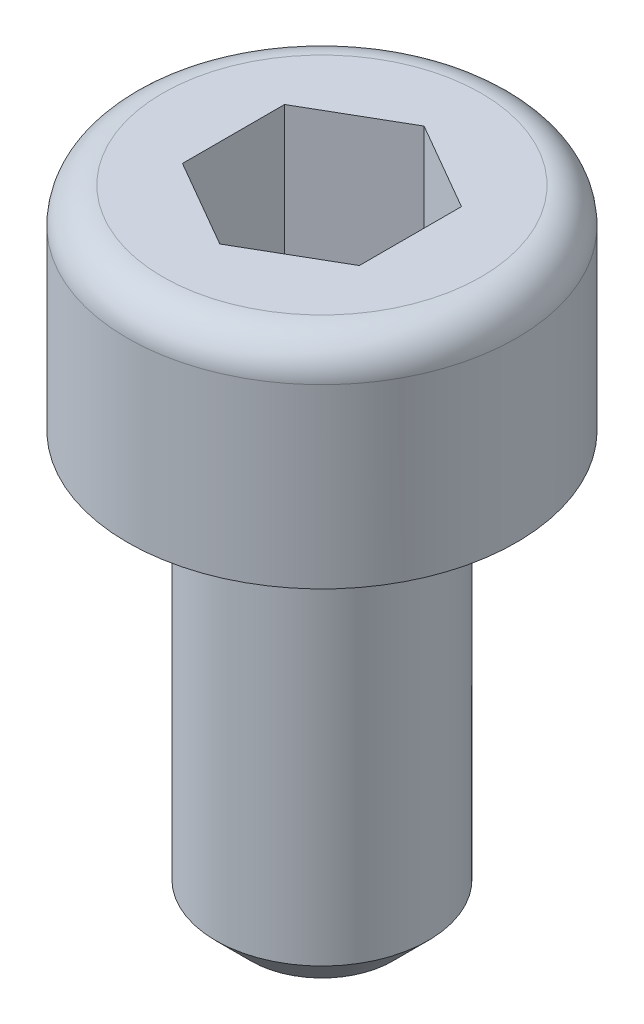
SolidWorks part; units mm, degrees
material "acero"
ref_plane "Alzado" through (0, 0, 0) normal (0, 0, 1) x (1, 0, 0)
ref_plane "Planta" through (0, 0, 0) normal (0, 1, 0) x (1, 0, 0)
ref_plane "Vista lateral" through (0, 0, 0) normal (1, 0, 0) x (0, 0, -1)
sketch "Croquis1" plane through (0, 0, 0) normal (0, 0, 1) x (1, 0, 0)
  line L0 (0, 0) -> (0, -60.9498) construction
  line L1 (0, 0) -> (2.75, 0)
  line L2 (2.75, 0) -> (2.75, -3)
  line L3 (2.75, -3) -> (1.5, -3)
  line L4 (1.5, -3) -> (1.5, -9)
  line L5 (1.5, -9) -> (0, -9)
  line L6 (0, -9) -> (0, 0)
  dimension "D1" = 6
  dimension "D2" = 3
  dimension "D3" = 5.5
  dimension "D4" = 3
revolve "Revolución1" add sketch "Croquis1" angle 360 about L0
sketch "Croquis2" plane through (0, 0, 0) normal (0, 1, 0) x (1, 0, 0)
  line L1 (1.25, 0.7217) -> (0, 1.4434)
  line L2 (0, 1.4434) -> (-1.25, 0.7217)
  line L3 (-1.25, 0.7217) -> (-1.25, -0.7217)
  line L4 (-1.25, -0.7217) -> (0, -1.4434)
  line L5 (0, -1.4434) -> (1.25, -0.7217)
  line L6 (1.25, -0.7217) -> (1.25, 0.7217)
  circle A0 centre (0, 0) radius 1.25 construction
  dimension "D1" = 2.5
extrude "Cortar-Extruir1" cut sketch "Croquis2" against normal blind 2
chamfer "Chaflán1" distance 0.5 angle 45 1 edges at (0, -9, 1.5)
fillet "Redondeo1" radius 0.5 1 edges at (0, 0, 2.75)
